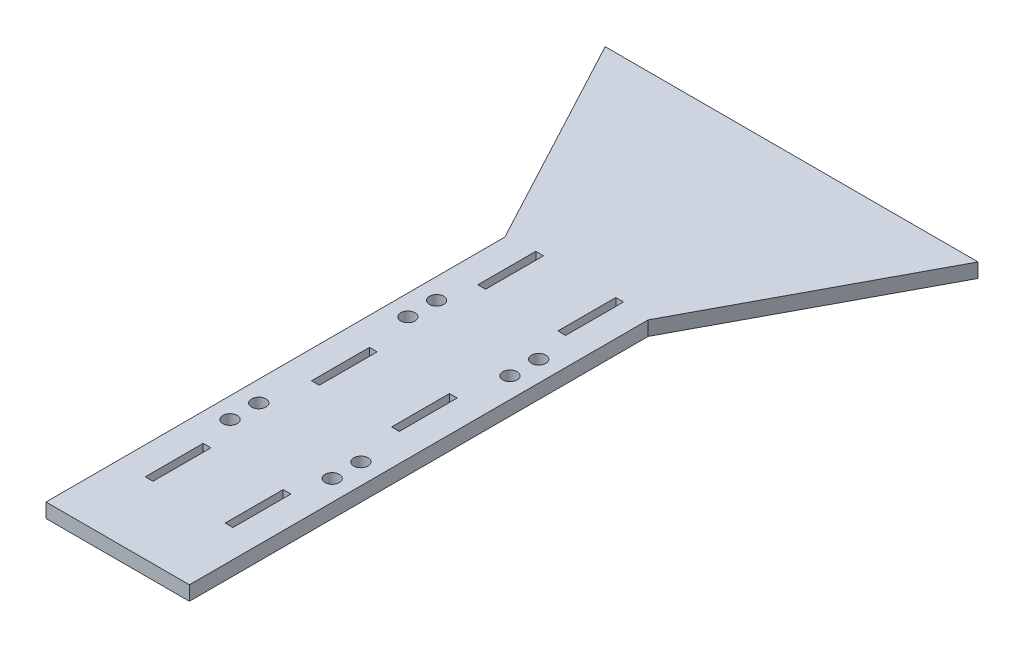
SolidWorks part; units mm, degrees
material "PC High Viscosity"
ref_plane "Front" through (0, 0, 0) normal (0, 0, 1) x (1, 0, 0)
ref_plane "Top" through (0, 0, 0) normal (0, 1, 0) x (1, 0, 0)
ref_plane "Right" through (0, 0, 0) normal (1, 0, 0) x (0, 0, -1)
sketch "Sketch1" plane through (0, 0, 0) normal (0, 1, 0) x (1, 0, 0)
  line L0 (-31.75, 0) -> (31.75, 0)
  line L1 (31.75, 0) -> (31.75, 203.2)
  line L2 (31.75, 203.2) -> (82.55, 298.45)
  line L3 (82.55, 298.45) -> (-82.55, 298.45)
  line L4 (-82.55, 298.45) -> (-31.75, 203.2)
  line L5 (-31.75, 203.2) -> (-31.75, 0)
  point P4 (0, 0)
  dimension "D1" = 63.5
  dimension "D2" = 203.2
  dimension "D3" = 95.25
  dimension "D4" = 165.1
extrude "Boss-Extrude1" add sketch "Sketch1" along normal blind 6.35
sketch "Sketch2" plane through (0, 6.35, 0) normal (0, 1, 0) x (1, 0, 0)
  line L4 (-19.431, 57.277) -> (-19.431, 31.623)
  line L5 (-19.431, 31.623) -> (-16.002, 31.623)
  line L6 (-16.002, 31.623) -> (-16.002, 57.277)
  line L7 (-16.002, 57.277) -> (-19.431, 57.277)
  line L8 (-19.431, 57.277) -> (-19.431, 31.623)
  line L9 (-19.431, 31.623) -> (-16.002, 31.623)
  line L10 (-16.002, 31.623) -> (-16.002, 57.277)
  line L11 (-16.002, 57.277) -> (-19.431, 57.277)
  line L12 (-19.431, 130.937) -> (-19.431, 105.283)
  line L13 (-19.431, 105.283) -> (-16.002, 105.283)
  line L14 (-16.002, 105.283) -> (-16.002, 130.937)
  line L15 (-16.002, 130.937) -> (-19.431, 130.937)
  line L16 (-19.431, 130.937) -> (-19.431, 105.283)
  line L17 (-19.431, 105.283) -> (-16.002, 105.283)
  line L18 (-16.002, 105.283) -> (-16.002, 130.937)
  line L19 (-16.002, 130.937) -> (-19.431, 130.937)
  line L24 (-19.431, 204.597) -> (-19.431, 178.943)
  line L25 (-19.431, 178.943) -> (-16.002, 178.943)
  line L26 (-16.002, 178.943) -> (-16.002, 204.597)
  line L27 (-16.002, 204.597) -> (-19.431, 204.597)
  line L28 (-19.431, 204.597) -> (-19.431, 178.943)
  line L29 (-19.431, 178.943) -> (-16.002, 178.943)
  line L30 (-16.002, 178.943) -> (-16.002, 204.597)
  line L31 (-16.002, 204.597) -> (-19.431, 204.597)
  line L36 (16.002, 204.597) -> (16.002, 178.943)
  line L37 (16.002, 178.943) -> (19.431, 178.943)
  line L38 (19.431, 178.943) -> (19.431, 204.597)
  line L39 (19.431, 204.597) -> (16.002, 204.597)
  line L40 (16.002, 204.597) -> (16.002, 178.943)
  line L41 (16.002, 178.943) -> (19.431, 178.943)
  line L42 (19.431, 178.943) -> (19.431, 204.597)
  line L43 (19.431, 204.597) -> (16.002, 204.597)
  line L48 (16.002, 130.937) -> (16.002, 105.283)
  line L49 (16.002, 105.283) -> (19.431, 105.283)
  line L50 (19.431, 105.283) -> (19.431, 130.937)
  line L51 (19.431, 130.937) -> (16.002, 130.937)
  line L52 (16.002, 130.937) -> (16.002, 105.283)
  line L53 (16.002, 105.283) -> (19.431, 105.283)
  line L54 (19.431, 105.283) -> (19.431, 130.937)
  line L55 (19.431, 130.937) -> (16.002, 130.937)
  line L60 (16.002, 57.277) -> (16.002, 31.623)
  line L61 (16.002, 31.623) -> (19.431, 31.623)
  line L62 (19.431, 31.623) -> (19.431, 57.277)
  line L63 (19.431, 57.277) -> (16.002, 57.277)
  line L64 (16.002, 57.277) -> (16.002, 31.623)
  line L65 (16.002, 31.623) -> (19.431, 31.623)
  line L66 (19.431, 31.623) -> (19.431, 57.277)
  line L67 (19.431, 57.277) -> (16.002, 57.277)
  dimension "D1" = 0.127
  dimension "D2" = 0.127
  dimension "D3" = 0.127
  dimension "D4" = 0.127
  dimension "D5" = 0.127
  dimension "D6" = 0.127
extrude "Cut-Extrude1" cut sketch "Sketch2" against normal through all
sketch "Sketch3" plane through (0, 6.35, 0) normal (0, 1, 0) x (1, 0, 0)
  line L0 (0, 298.45) -> (0, 157.48) construction
  line L1 (82.55, 298.45) -> (-82.55, 298.45) construction
  line L2 (0, 157.48) -> (-31.75, 157.48) construction
  line L3 (-31.75, 203.2) -> (-31.75, 0) construction
  line L4 (-19.431, 204.597) -> (-19.431, 178.943) construction
  line L6 (-19.431, 118.11) -> (19.431, 118.11) construction
  line L7 (-19.431, 130.937) -> (-19.431, 105.283) construction
  line L8 (19.431, 105.283) -> (19.431, 130.937) construction
  circle A0 centre (-22.606, 163.83) radius 3.175
  circle A1 centre (-22.606, 151.13) radius 3.175
  circle A2 centre (22.606, 151.13) radius 3.175
  circle A3 centre (22.606, 163.83) radius 3.175
  circle A4 centre (22.606, 85.09) radius 3.175
  circle A5 centre (22.606, 72.39) radius 3.175
  circle A6 centre (-22.606, 72.39) radius 3.175
  circle A7 centre (-22.606, 85.09) radius 3.175
  dimension "D2" = 6.35
  dimension "D1" = 140.97
  dimension "D3" = 6.35
extrude "Cut-Extrude2" cut sketch "Sketch3" against normal through all
